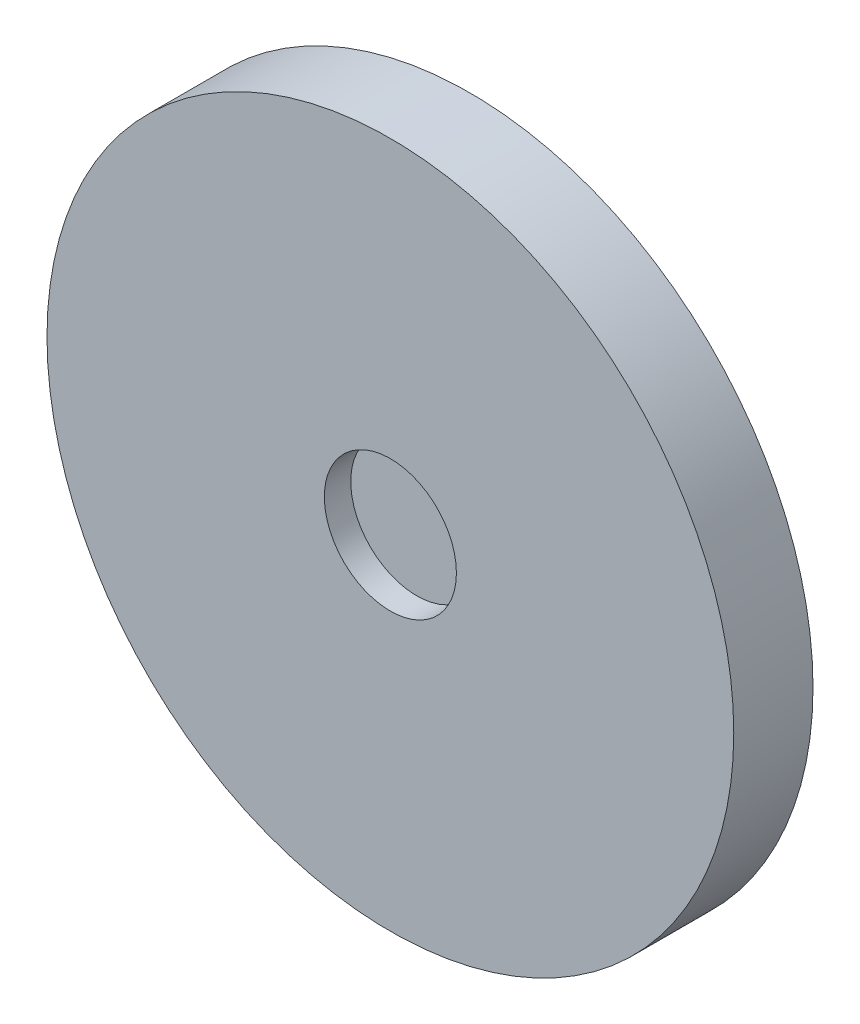
SolidWorks part; units mm, degrees
ref_plane "Front Plane" through (0, 0, 0) normal (0, 0, 1) x (1, 0, 0)
ref_plane "Top Plane" through (0, 0, 0) normal (0, 1, 0) x (1, 0, 0)
ref_plane "Right Plane" through (0, 0, 0) normal (1, 0, 0) x (0, 0, -1)
sketch "Sketch1" plane through (0, 0, 0) normal (0, 0, 1) x (1, 0, 0)
  circle A0 centre (0, 0) radius 3.9
  dimension "D1" = 7.8
extrude "Boss-Extrude1" add sketch "Sketch1" along normal blind 0.9
sketch "Sketch2" plane through (0, 0, 0.9) normal (0, 0, 1) x (1, 0, 0)
  circle A0 centre (0, 0) radius 0.75
  dimension "D1" = 1.5
extrude "Cut-Extrude1" cut sketch "Sketch2" against normal blind 0.3
